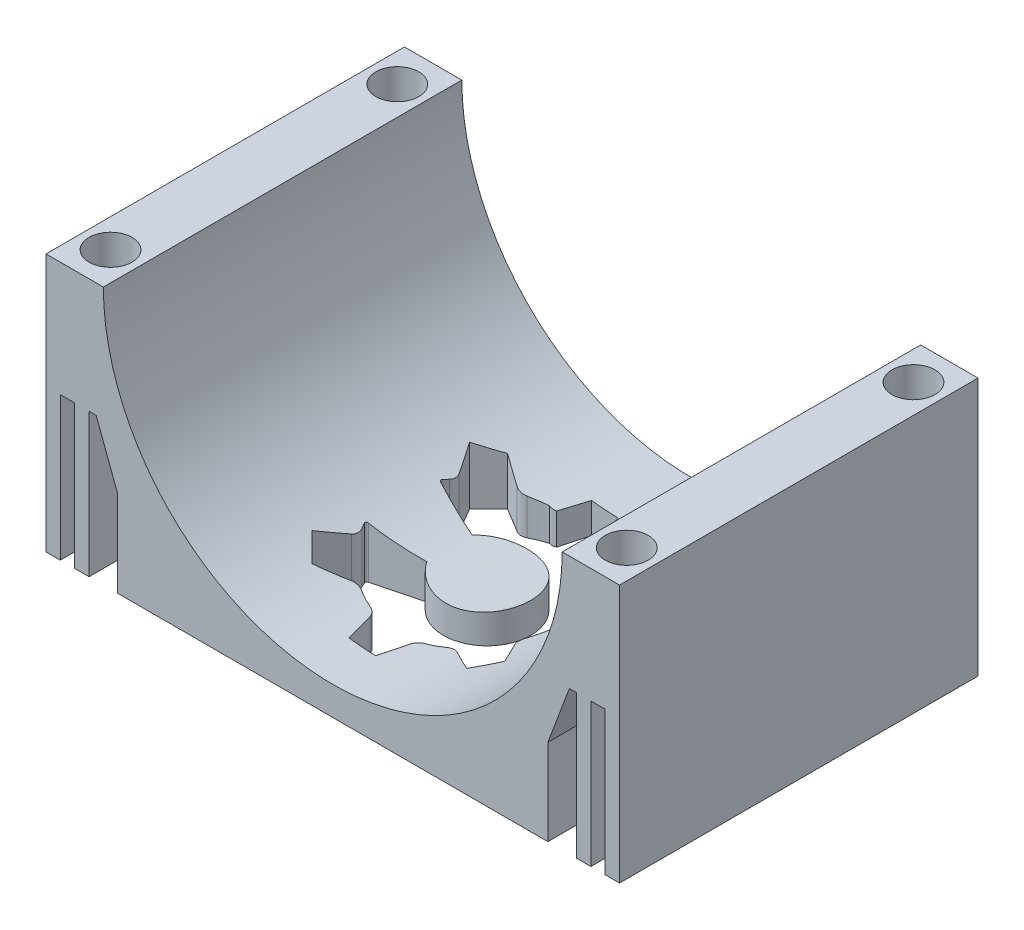
SolidWorks part; units mm, degrees
ref_plane "Alzado" through (0, 0, 0) normal (0, 0, 1) x (1, 0, 0)
ref_plane "Planta" through (0, 0, 0) normal (0, 1, 0) x (1, 0, 0)
ref_plane "Vista lateral" through (0, 0, 0) normal (1, 0, 0) x (0, 0, -1)
sketch "Croquis1" plane through (0, 0, 0) normal (0, 1, 0) x (1, 0, 0)
  line L1 (0, 0) -> (40, 0)
  line L2 (0, 0) -> (0, 25)
  line L3 (0, 25) -> (40, 25)
  line L4 (40, 0) -> (40, 25)
  dimension "D1" = 40
  dimension "D2" = 25
extrude "Saliente-Extruir1" add sketch "Croquis1" along normal blind 18
sketch "Croquis2" plane through (0, 0, 0) normal (0, 0, 1) x (1, 0, 0)
  line L0 (0, 18) -> (40, 18) construction
  circle A0 centre (20, 18) radius 16
  dimension "D1" = 32
extrude "Cortar-Extruir1" cut sketch "Croquis2" against normal through all
sketch "Croquis3" plane through (0, 18, 0) normal (0, 1, 0) x (1, 0, 0)
  line L0 (0, 0) -> (4, 0) construction
  line L3 (40, 25) -> (36, 25) construction
  line L4 (36, 0) -> (40, 0) construction
  line L5 (4, 25) -> (0, 25) construction
  circle A0 centre (2, 2.5) radius 1.5
  circle A1 centre (2, 22.5) radius 1.5
  circle A2 centre (38, 2.5) radius 1.5
  circle A4 centre (38, 22.5) radius 1.5
  dimension "D1" = 3
  dimension "D3" = 3
  dimension "D4" = 3
  dimension "D5" = 3
  dimension "D2" = 2.5
  dimension "D6" = 2.5
  dimension "D7" = 2.5
  dimension "D8" = 2.5
extrude "Cortar-Extruir2" cut sketch "Croquis3" against normal through all
sketch "Croquis4" plane through (0, 0, 0) normal (0, -1, 0) x (1, 0, 0)
  line L0 (18.9001, 13.1368) -> (18.9001, -36.8632) construction
  line L1 (12.0882, -6.4785) -> (13.4016, -5.1429)
  line L2 (17.8909, -3.239) -> (19.7641, -3.2232)
  line L3 (24.2848, -5.0514) -> (25.6204, -6.3648)
  line L4 (27.5243, -10.854) -> (27.5401, -12.7272)
  line L5 (25.712, -17.2479) -> (24.3986, -18.5836)
  line L6 (13.1097, -14.4154) -> (16.2841, -13.4347)
  line L7 (12.0882, -6.4785) -> (13.12, -8.1848)
  line L8 (19.9093, -20) -> (18.0361, -20.0158)
  line L9 (13.5154, -18.6751) -> (12.1798, -17.3617)
  line L10 (13.4016, -5.1429) -> (15.125, -6.1458)
  line L11 (17.8909, -3.239) -> (17.414, -5.175)
  line L12 (19.7641, -3.2232) -> (20.2735, -5.151)
  line L13 (24.2848, -5.0514) -> (22.5786, -6.0831)
  line L14 (25.6204, -6.3648) -> (24.6175, -8.0881)
  line L15 (27.5243, -10.854) -> (25.5883, -10.3771)
  line L16 (27.5401, -12.7272) -> (25.6123, -13.2366)
  line L17 (25.712, -17.2479) -> (24.6802, -15.5417)
  line L18 (24.3986, -18.5836) -> (22.6752, -17.5806)
  line L19 (19.9093, -20) -> (20.3862, -18.0639)
  line L20 (18.0361, -20.0158) -> (17.5267, -18.088)
  line L21 (13.5154, -18.6751) -> (15.2216, -17.6433)
  line L22 (12.1798, -17.3617) -> (13.1827, -15.6384)
  line L23 (16.3067, -10.2548) -> (13.0707, -9.4109)
  line L24 (5, -20) -> (5, -25)
  line L25 (38.9001, -11.8632) -> (-1.0999, -11.8632) construction
  line L26 (0, 0) -> (5, 0)
  line L27 (0, 0) -> (0, -5)
  line L28 (5, 0) -> (5, -5)
  line L29 (0, -20) -> (0, -25)
  line L30 (0, -25) -> (5, -25)
  line L31 (35, 0) -> (35, -5)
  line L32 (40, -5) -> (40, 0)
  line L33 (40, 0) -> (35, 0)
  line L34 (35, -20) -> (35, -25)
  line L35 (35, -25) -> (40, -25)
  line L36 (40, -25) -> (40, -20)
  line L37 (5, -5) -> (5, -20)
  line L38 (0, -5) -> (0, -20)
  line L39 (35, -5) -> (35, -20)
  line L40 (40, -5) -> (40, -20)
  arc A0 (20.8668, -18.0376) -> (21.9718, -17.5689) centre (18.9001, -11.8632) ccw
  arc A1 (13.0271, -14.6015) -> (13.1944, -14.9349) centre (18.9001, -11.8632) ccw
  arc A2 (13.1097, -14.4154) -> (13.0271, -14.6015) centre (13.1496, -14.5444) ccw
  arc A3 (12.9814, -9.2252) -> (13.0707, -9.4109) centre (13.1048, -9.2802) ccw
  arc A4 (15.8284, -6.1575) -> (15.125, -6.1458) centre (15.4871, -5.5235) cw
  arc A5 (13.1435, -8.8879) -> (13.12, -8.1848) centre (12.5039, -8.5573) ccw
  arc A6 (20.7626, -5.6567) -> (20.2735, -5.151) centre (20.9696, -4.967) cw
  arc A7 (16.9334, -5.6889) -> (17.414, -5.175) centre (16.7149, -5.0028) ccw
  arc A8 (24.6058, -8.7915) -> (24.6175, -8.0881) centre (25.2398, -8.4502) cw
  arc A9 (21.8754, -6.1066) -> (22.5786, -6.0831) centre (22.206, -5.467) ccw
  arc A10 (25.1067, -13.7258) -> (25.6123, -13.2366) centre (25.7963, -13.9327) cw
  arc A11 (25.0745, -9.8966) -> (25.5883, -10.3771) centre (25.7605, -9.678) ccw
  arc A12 (21.9718, -17.5689) -> (22.6752, -17.5806) centre (22.3131, -18.2029) cw
  arc A13 (24.6567, -14.8385) -> (24.6802, -15.5417) centre (25.2963, -15.1691) ccw
  arc A14 (17.0376, -18.0698) -> (17.5267, -18.088) centre (17.2569, -18.7555) cw
  arc A15 (20.8668, -18.0376) -> (20.3862, -18.0639) centre (20.6636, -18.7283) ccw
  arc A16 (13.1944, -14.9349) -> (13.1827, -15.6384) centre (12.5604, -15.2762) cw
  arc A17 (15.9248, -17.6198) -> (15.2216, -17.6433) centre (15.5942, -18.2594) ccw
  arc A18 (15.9248, -17.6198) -> (17.0376, -18.0698) centre (18.9001, -11.8632) ccw
  arc A19 (13.1435, -8.8879) -> (12.9814, -9.2252) centre (18.9001, -11.8632) ccw
  arc A20 (16.9334, -5.6889) -> (15.8284, -6.1575) centre (18.9001, -11.8632) ccw
  arc A21 (21.8754, -6.1066) -> (20.7626, -5.6567) centre (18.9001, -11.8632) ccw
  arc A22 (25.0745, -9.8966) -> (24.6058, -8.7915) centre (18.9001, -11.8632) ccw
  arc A23 (24.6567, -14.8385) -> (25.1067, -13.7258) centre (18.9001, -11.8632) ccw
  arc A24 (16.2841, -13.4347) -> (16.3067, -10.2548) centre (18.9001, -11.8632) ccw
extrude "Cortar-Extruir3" cut sketch "Croquis4" against normal blind 10
sketch "Croquis5" plane through (0, 0, -25) normal (0, 0, -1) x (-1, 0, 0)
  line L0 (-5, 10) -> (-5, 6)
  line L1 (-5, 10) -> (-5, 0) construction
  line L2 (-5, 10) -> (-3.5, 10)
  line L3 (0, 10) -> (-5, 10) construction
  line L4 (-3.5, 10) -> (-5, 6)
  line L5 (-35, 10) -> (-35, 6)
  line L6 (-35, 10) -> (-35, 0) construction
  line L7 (-35, 10) -> (-36.5, 10)
  line L8 (-35, 10) -> (-40, 10) construction
  line L9 (-36.5, 10) -> (-35, 6)
  dimension "D1" = 4
  dimension "D2" = 1.5
  dimension "D3" = 4
  dimension "D4" = 1.5
extrude "Saliente-Extruir2" add sketch "Croquis5" against normal up to surface (25 mm away) up to face at (20, 9.6, 0)
sketch "Croquis6" plane through (0, 10, 0) normal (0, -1, 0) x (1, 0, 0)
  line L0 (0, 0) -> (0, -25)
  line L1 (40, 0) -> (40, -25)
  line L2 (1, 0) -> (1, -25)
  line L3 (2, 0) -> (2, -25)
  line L4 (3, 0) -> (3, -25)
  line L5 (39, 0) -> (39, -25)
  line L6 (38, 0) -> (38, -25)
  line L7 (37, 0) -> (37, -25)
  line L8 (0, 0) -> (1, 0)
  line L9 (2, 0) -> (3, 0)
  line L10 (0, -25) -> (1, -25)
  line L11 (2, -25) -> (3, -25)
  line L12 (37, 0) -> (38, 0)
  line L13 (39, 0) -> (40, 0)
  line L14 (37, -25) -> (38, -25)
  line L15 (39, -25) -> (40, -25)
  dimension "D1" = 4
  dimension "D2" = 4
extrude "Saliente-Extruir3" add sketch "Croquis6" along normal up to surface (10 mm away) up to face at (20, 0, -12.5)
